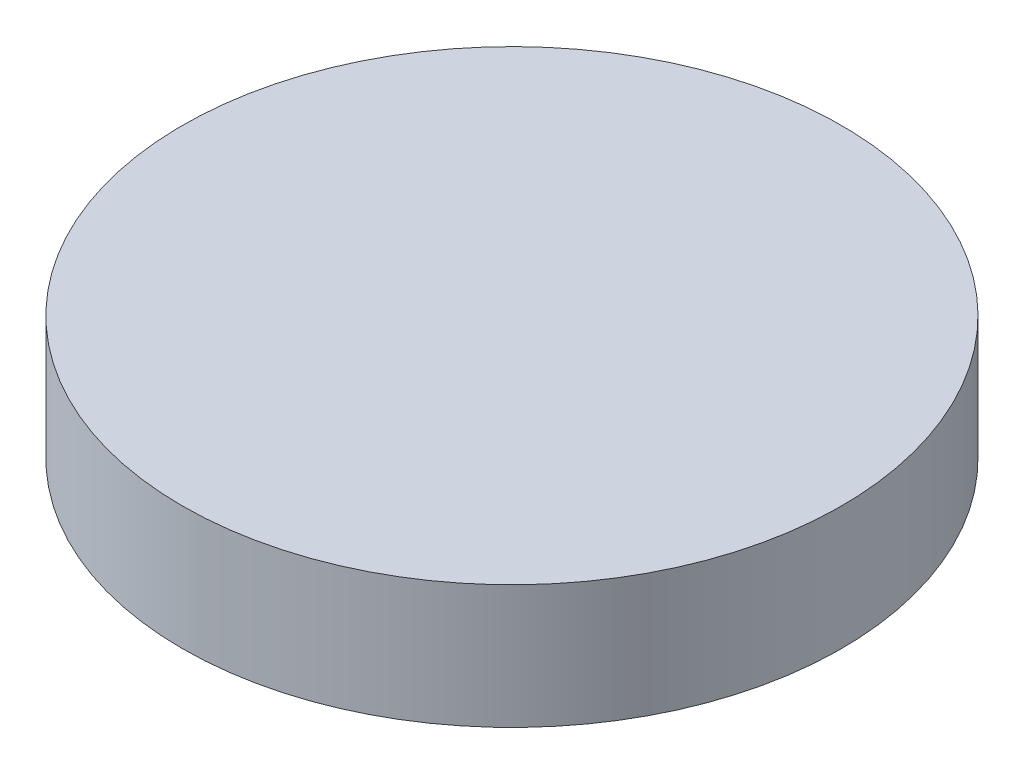
SolidWorks part; units mm, degrees
ref_plane "Front Plane" through (0, 0, 0) normal (0, 0, 1) x (1, 0, 0)
ref_plane "Top Plane" through (0, 0, 0) normal (0, 1, 0) x (1, 0, 0)
ref_plane "Right Plane" through (0, 0, 0) normal (1, 0, 0) x (0, 0, -1)
sketch "Sketch1" plane through (0, 0, 0) normal (0, 1, 0) x (1, 0, 0)
  circle A0 centre (0, 0) radius 20
  dimension "D1" = 40
extrude "Boss-Extrude1" add sketch "Sketch1" along normal blind 7.5
